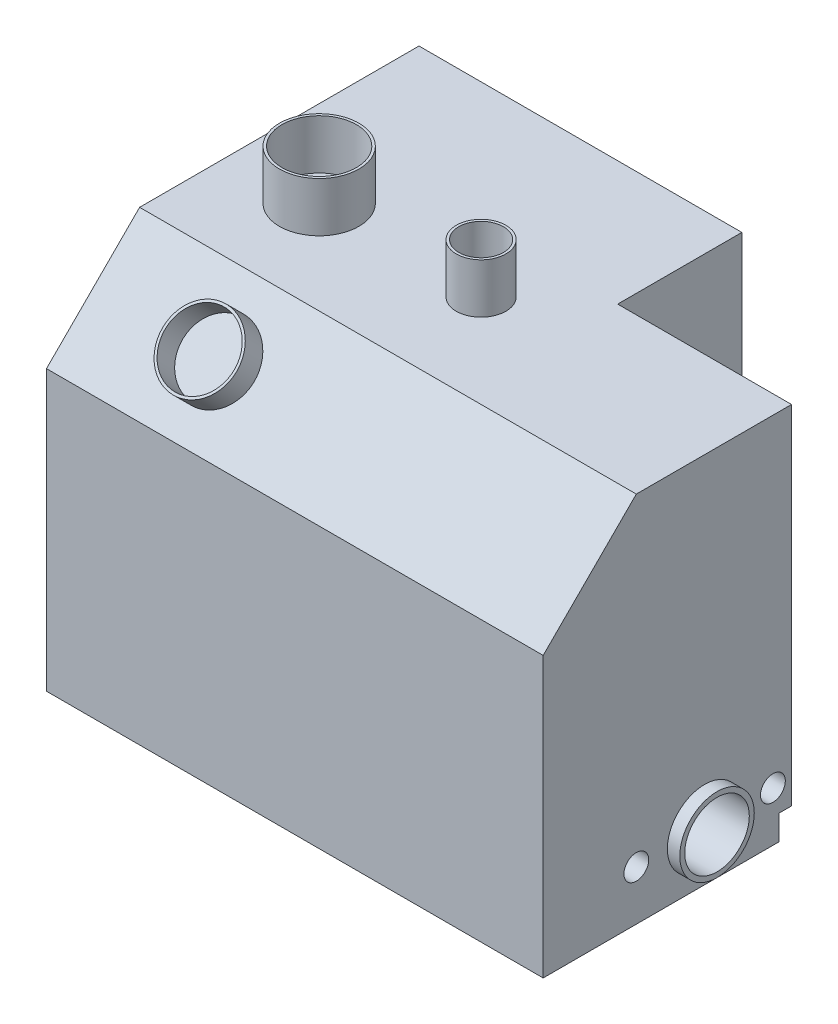
SolidWorks part; units mm, degrees
material "Plain Carbon Steel"
ref_plane "Front Plane" through (0, 0, 0) normal (0, 0, 1) x (1, 0, 0)
ref_plane "Top Plane" through (0, 0, 0) normal (0, 1, 0) x (1, 0, 0)
ref_plane "Right Plane" through (0, 0, 0) normal (1, 0, 0) x (0, 0, -1)
sketch "Sketch1" plane through (0, 0, 0) normal (0, 1, 0) x (1, 0, 0)
  line L1 (100, -75) -> (-100, -75)
  line L2 (100, -75) -> (100, 75)
  line L3 (100, 75) -> (-100, 75)
  line L4 (-100, -75) -> (-100, 75)
  line L5 (100, -75) -> (-100, 75) construction
  line L6 (100, 75) -> (-100, -75) construction
  point P0 (0, 0)
  dimension "D1" = 200
  dimension "D2" = 150
extrude "Boss-Extrude1" add sketch "Sketch1" along normal blind 150
sketch "Sketch2" plane through (100, 0, 0) normal (1, 0, 0) x (0, 0, -1)
  line L0 (0, 0) -> (0, 150) construction
  line L1 (-75, 150) -> (75, 150) construction
  line L2 (0, 150) -> (-10, 150) construction
  line L3 (-10, 150) -> (-10, 0) construction
  line L4 (-75, 0) -> (75, 0) construction
  line L5 (-75, 20) -> (75, 20) construction
  line L6 (-75, 150) -> (-75, 0) construction
  line L7 (75, 150) -> (75, 0) construction
  circle A0 centre (-10, 20) radius 15
  circle A1 centre (-10, 20) radius 13
  dimension "D1" = 10
  dimension "D2" = 20
extrude "Boss-Extrude2" add sketch "Sketch2" along normal blind 5
sketch "Sketch3" plane through (100, 0, 0) normal (1, 0, 0) x (0, 0, -1)
  line L0 (-10, 20) -> (-75, 20) construction
  line L1 (-75, 150) -> (-75, 0) construction
  line L2 (-10, 33) -> (-10, 7) construction
  line L3 (75, 150) -> (75, 0) construction
  line L4 (75, 10) -> (20, 10)
  line L5 (75, 10) -> (75, 0)
  line L7 (20, 10) -> (20, 0)
  line L8 (-75, 0) -> (75, 0) construction
  line L11 (20, 0) -> (20, -30)
  line L12 (20, -30) -> (75, -30)
  line L13 (75, 0) -> (75, -30)
  circle A0 centre (-10, 20) radius 13
  circle A1 centre (-37.5, 20) radius 5
  circle A2 centre (17.5, 20) radius 5
  dimension "D1" = 27.5
  dimension "D2" = 55
  dimension "D3" = 10
  dimension "D4" = 30
extrude "Cut-Extrude1" cut sketch "Sketch3" against normal blind 70
sketch "Sketch4" plane through (100, 0, 0) normal (1, 0, 0) x (0, 0, -1)
  line L0 (0, 150) -> (-75, 150) construction
  line L1 (-75, 150) -> (75, 150) construction
  line L2 (-37.5, 150) -> (-75, 112.5)
  line L3 (-75, 150) -> (-75, 0) construction
  line L4 (-37.5, 150) -> (-75, 150)
  line L5 (-75, 150) -> (-75, 112.5)
extrude "Cut-Extrude2" cut sketch "Sketch4" against normal through all
sketch "Sketch5" plane through (0, 93.75, 93.75) normal (0, 0.7071, 0.7071) x (1, 0, 0)
  line L0 (0, 26.5165) -> (0, 79.5495) construction
  line L1 (-100, 26.5165) -> (100, 26.5165) construction
  line L2 (-100, 79.5495) -> (100, 79.5495) construction
  line L3 (0, 79.5495) -> (0, 53.033) construction
  line L4 (0, 53.033) -> (-100, 53.033) construction
  line L5 (-50, 53.033) -> (-50, 79.5495) construction
  circle A0 centre (-50, 53.033) radius 15
  circle A1 centre (-50, 53.033) radius 14
extrude "Boss-Extrude3" add sketch "Sketch5" along normal blind 10
sketch "Sketch7" plane through (0, 150, 0) normal (0, 1, 0) x (1, 0, 0)
  line L0 (0, 0) -> (100, 0) construction
  line L1 (100, -37.5) -> (100, 75) construction
  circle A0 centre (0, 0) radius 10
  circle A1 centre (0, 0) radius 9
  circle A2 centre (-65.196, 0) radius 15
  circle A3 centre (-65.196, 0) radius 16
  dimension "D1" = 20
  dimension "D2" = 32
  dimension "D3" = 30
extrude "Boss-Extrude4" add sketch "Sketch7" along normal blind 20
sketch "Sketch10" plane through (0, 150, 0) normal (0, 1, 0) x (1, 0, 0)
  line L1 (100, 75) -> (30, 75)
  line L2 (100, 75) -> (100, 25)
  line L3 (100, 25) -> (30, 25)
  line L4 (30, 75) -> (30, 25)
  dimension "D1" = 50
  dimension "D2" = 70
extrude "Cut-Extrude5" cut sketch "Sketch10" against normal through all
